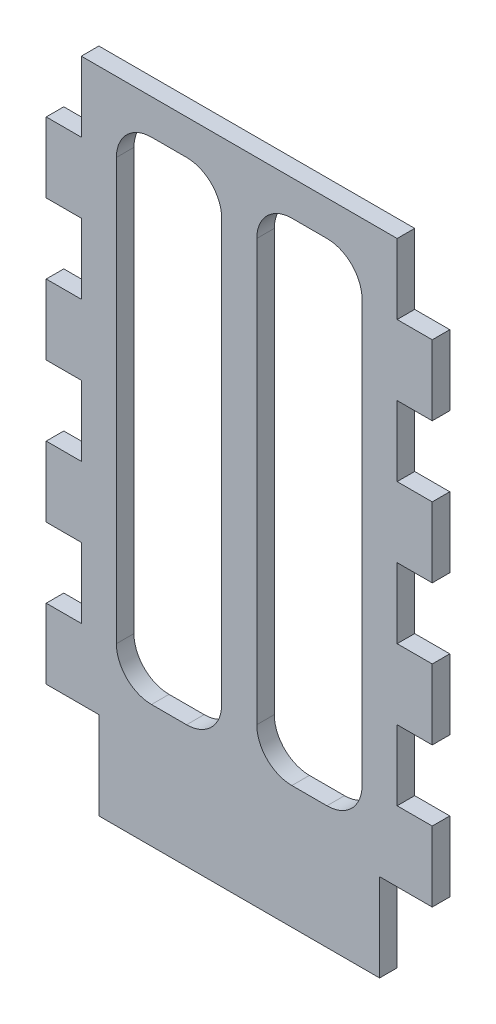
SolidWorks part; units mm, degrees
ref_plane "Front Plane" through (0, 0, 0) normal (0, 0, 1) x (1, 0, 0)
ref_plane "Top Plane" through (0, 0, 0) normal (0, 1, 0) x (1, 0, 0)
ref_plane "Right Plane" through (0, 0, 0) normal (1, 0, 0) x (0, 0, -1)
sketch "Sketch1" plane through (0, 0, 0) normal (0, 0, 1) x (1, 0, 0)
  line L1 (0, 0) -> (57.15, 0)
  line L2 (0, 0) -> (0, -101.6)
  line L3 (0, -101.6) -> (57.15, -101.6)
  line L4 (57.15, 0) -> (57.15, -101.6)
  dimension "D1" = 57.15
  dimension "D2" = 101.6
extrude "Boss-Extrude1" add sketch "Sketch1" along normal blind 3.175
sketch "Sketch2" plane through (0, 0, 3.175) normal (0, 0, 1) x (1, 0, 0)
  line L0 (57.15, -101.6) -> (57.15, 0) construction
  line L1 (57.15, -12.7) -> (63.5, -12.7)
  line L2 (57.15, -12.7) -> (57.15, -25.4)
  line L3 (57.15, -25.4) -> (63.5, -25.4)
  line L4 (63.5, -12.7) -> (63.5, -25.4)
  line L5 (0, 0) -> (0, -101.6) construction
  line L6 (0, -12.7) -> (-6.35, -12.7)
  line L7 (0, -12.7) -> (0, -25.4)
  line L8 (0, -25.4) -> (-6.35, -25.4)
  line L9 (-6.35, -12.7) -> (-6.35, -25.4)
  line L10 (57.15, 0) -> (0, 0) construction
  dimension "D1" = 6.35
  dimension "D2" = 6.35
  dimension "D3" = 12.7
  dimension "D4" = 12.7
  dimension "D5" = 12.7
  dimension "D6" = 12.7
extrude "Boss-Extrude2" add sketch "Sketch2" against normal blind 3.175
pattern_linear "LPattern1" count 4 spacing 25.4 along (0, -1, 0) of "Boss-Extrude2"
sketch "Sketch3" plane through (0, 0, 3.175) normal (0, 0, 1) x (1, 0, 0)
  line L0 (-6.35, -101.6) -> (63.5, -101.6) construction
  line L1 (3.175, -101.6) -> (53.975, -101.6)
  line L2 (3.175, -101.6) -> (3.175, -117.475)
  line L3 (3.175, -117.475) -> (53.975, -117.475)
  line L4 (53.975, -101.6) -> (53.975, -117.475)
  line L5 (0, -50.8) -> (0, -63.5) construction
  dimension "D1" = 50.8
  dimension "D2" = 15.875
  dimension "D3" = 3.175
extrude "Boss-Extrude3" add sketch "Sketch3" against normal blind 3.175
sketch "Sketch4" plane through (0, 0, 3.175) normal (0, 0, 1) x (1, 0, 0)
  line L0 (0, 0) -> (0, -12.7) construction
  line L1 (6.35, -6.35) -> (25.4, -6.35)
  line L2 (6.35, -6.35) -> (6.35, -95.25)
  line L3 (6.35, -95.25) -> (25.4, -95.25)
  line L4 (25.4, -6.35) -> (25.4, -95.25)
  line L5 (50.8, -6.35) -> (31.75, -6.35)
  line L6 (50.8, -6.35) -> (50.8, -95.25)
  line L7 (50.8, -95.25) -> (31.75, -95.25)
  line L8 (31.75, -6.35) -> (31.75, -95.25)
  line L9 (57.15, -12.7) -> (57.15, 0) construction
  line L10 (57.15, 0) -> (0, 0) construction
  line L11 (-6.35, -101.6) -> (3.175, -101.6) construction
  line L12 (53.975, -101.6) -> (63.5, -101.6) construction
  dimension "D1" = 19.05
  dimension "D2" = 19.05
  dimension "D3" = 6.35
  dimension "D4" = 6.35
  dimension "D5" = 6.35
  dimension "D6" = 6.35
  dimension "D7" = 6.35
  dimension "D8" = 6.35
extrude "Cut-Extrude1" cut sketch "Sketch4" against normal blind 3.175
fillet "Fillet1" radius 6.35 8 edges at (25.4, -95.25, 1.5875) (50.8, -95.25, 1.5875) (31.75, -95.25, 1.5875) (6.35, -95.25, 1.5875) (50.8, -6.35, 1.5875) (25.4, -6.35, 1.5875) (31.75, -6.35, 1.5875) (6.35, -6.35, 1.5875)
